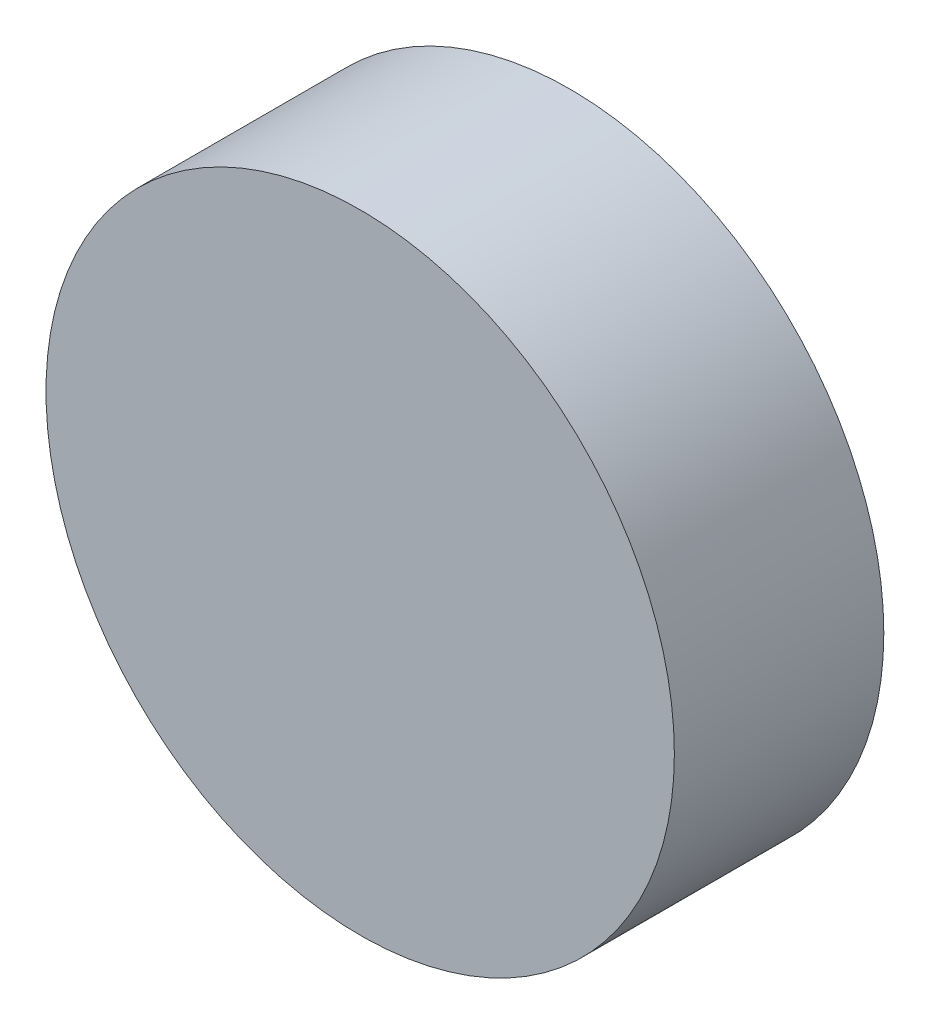
SolidWorks part; units mm, degrees
material "6061 Alloy"
ref_plane "Front Plane" through (0, 0, 0) normal (0, 0, 1) x (1, 0, 0)
ref_plane "Top Plane" through (0, 0, 0) normal (0, 1, 0) x (1, 0, 0)
ref_plane "Right Plane" through (0, 0, 0) normal (1, 0, 0) x (0, 0, -1)
sketch "Wheel Cross Section" plane through (0, 0, 0) normal (0, 0, 1) x (1, 0, 0)
  circle A0 centre (0, 0) radius 152.4
  dimension "D1" = 304.8
extrude "Drive Wheel" add sketch "Wheel Cross Section" along normal mid plane 101.6
